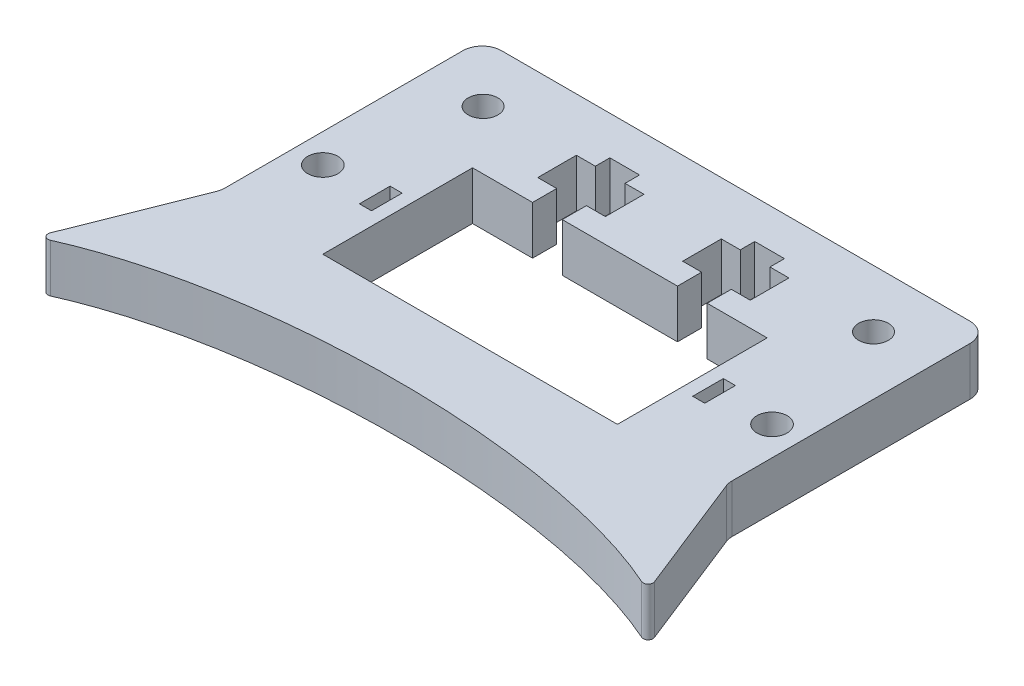
SolidWorks part; units mm, degrees
ref_plane "Front Plane" through (0, 0, 0) normal (0, 0, 1) x (1, 0, 0)
ref_plane "Top Plane" through (0, 0, 0) normal (0, 1, 0) x (1, 0, 0)
ref_plane "Right Plane" through (0, 0, 0) normal (1, 0, 0) x (0, 0, -1)
sketch "Sketch1" plane through (0, 0, 0) normal (0, 1, 0) x (1, 0, 0)
  line L1 (-52.5, -35) -> (52.5, -35)
  line L2 (-52.5, -35) -> (-52.5, 35)
  line L3 (-52.5, 35) -> (52.5, 35)
  line L4 (52.5, -35) -> (52.5, 35)
  line L5 (0, 35) -> (0, -35) construction
  line L6 (-52.5, 0) -> (52.5, 0) construction
  point P0 (0, 0)
  dimension "D1" = 105
  dimension "D2" = 70
extrude "Boss-Extrude1" add sketch "Sketch1" along normal blind 10
sketch "Sketch2" plane through (0, 10, 0) normal (0, 1, 0) x (1, 0, 0)
  line L6 (-30.5, 11) -> (30.5, 11)
  line L7 (-30.5, 11) -> (-30.5, -20)
  line L8 (-30.5, -20) -> (30.5, -20)
  line L9 (30.5, 11) -> (30.5, -20)
  line L10 (0, -20) -> (0, 11) construction
  line L11 (-30.5, -4.5) -> (30.5, -4.5) construction
  line L12 (0, 0) -> (0, -20) construction
  line L14 (-52.5, -35) -> (52.5, -35) construction
  point P0 (0, -4.5)
  dimension "D1" = 31
  dimension "D2" = 61
  dimension "D3" = 15
extrude "Cut-Extrude1" cut sketch "Sketch2" against normal through all
sketch "Sketch3" plane through (0, 10, 0) normal (0, 1, 0) x (1, 0, 0)
  line L0 (-15, 35) -> (-15, 11.6634) construction
  line L1 (52.5, 35) -> (-52.5, 35) construction
  line L3 (-22, 24) -> (-22, 16)
  line L4 (-18.075, 7.3268) -> (-11.925, 7.3268)
  line L5 (-18.075, 7.3268) -> (-18.075, 16)
  line L6 (-18.075, 16) -> (-11.925, 16)
  line L7 (-11.925, 7.3268) -> (-11.925, 16)
  line L8 (-15, 16) -> (-15, 7.3268) construction
  line L9 (-18.075, 11.6634) -> (-11.925, 11.6634) construction
  line L10 (-22, 24) -> (-8, 24)
  line L11 (-22, 16) -> (-8, 16)
  line L12 (-8, 24) -> (-8, 16)
  line L13 (-15, 16) -> (-15, 24) construction
  line L14 (-22, 20) -> (-8, 20) construction
  line L15 (0, 0) -> (0, 35) construction
  line L16 (-11.925, 21) -> (-18.075, 21)
  line L17 (-11.925, 21) -> (-11.925, 27)
  line L18 (-11.925, 27) -> (-18.075, 27)
  line L19 (-18.075, 21) -> (-18.075, 27)
  line L20 (-15, 27) -> (-15, 21) construction
  line L21 (-11.925, 24) -> (-18.075, 24) construction
  line L22 (30.5, 11) -> (-30.5, 11) construction
  point P10 (-15, 20)
  dimension "D1" = 6.15
  dimension "D2" = 5
  dimension "D3" = 14
  dimension "D4" = 8
  dimension "D5" = 16
  dimension "D6" = 15
extrude "Cut-Extrude2" cut sketch "Sketch3" against normal blind 10
sketch "Sketch4" plane through (0, 10, 0) normal (0, 1, 0) x (1, 0, 0)
  line L2 (-46.5, -4) -> (-34.5, -4) construction
  line L3 (-18.075, 11) -> (-30.5, 11) construction
  line L4 (-33.25, -0.825) -> (-35.75, -0.825)
  line L5 (-33.25, -0.825) -> (-33.25, -7.175)
  line L6 (-33.25, -7.175) -> (-35.75, -7.175)
  line L7 (-35.75, -0.825) -> (-35.75, -7.175)
  line L8 (-34.5, -7.175) -> (-34.5, -0.825) construction
  line L9 (-33.25, -4) -> (-35.75, -4) construction
  line L10 (-30.5, 11) -> (-30.5, -20) construction
  circle A0 centre (-46.5, -4) radius 3.125
  dimension "D1" = 6.25
  dimension "D2" = 15
  dimension "D3" = 16
  dimension "D4" = 2.5
  dimension "D5" = 6.35
  dimension "D6" = 2.75
extrude "Cut-Extrude3" cut sketch "Sketch4" against normal through all
sketch "Sketch5" plane through (0, 0, 0) normal (0, 1, 0) x (1, 0, 0)
  line L0 (0, 0) -> (0, -65) construction
  line L1 (-52.5, -35) -> (52.5, -35) construction
  line L2 (-52.5, -19.0391) -> (-63.479, -46.7424)
  line L3 (-52.5, 35) -> (-52.5, -35) construction
  line L4 (-52.5, -19.0391) -> (0, -35)
  ellipse E0 centre (0, -65) end of major axis (-80, -65) minor radius 30
  dimension "D1" = 160
  dimension "D2" = 65
extrude "Boss-Extrude2" add sketch "Sketch5" along normal up to surface (10 mm away) contours E0 L4 L2 up to face at (-46.5, 10, 7.125)
sketch "Sketch6" plane through (0, 10, 0) normal (0, 1, 0) x (1, 0, 0)
  circle A0 centre (-40.4209, 23.095) radius 3.075
  dimension "D1" = 6.15
extrude "Cut-Extrude4" cut sketch "Sketch6" against normal through all
mirror "Mirror1" about plane through (0, 0, 0) normal (1, 0, 0) of "Cut-Extrude4", "Cut-Extrude3", "Cut-Extrude2", "Boss-Extrude2"
fillet "Fillet2" radius 1 2 edges at (-63.479, 5, 46.7424) (63.479, 5, 46.7424)
fillet "Fillet1" radius 4 4 edges at (-52.5, 5, 19.0391) (-52.5, 5, -35) (52.5, 5, 19.0391) (52.5, 5, -35)
